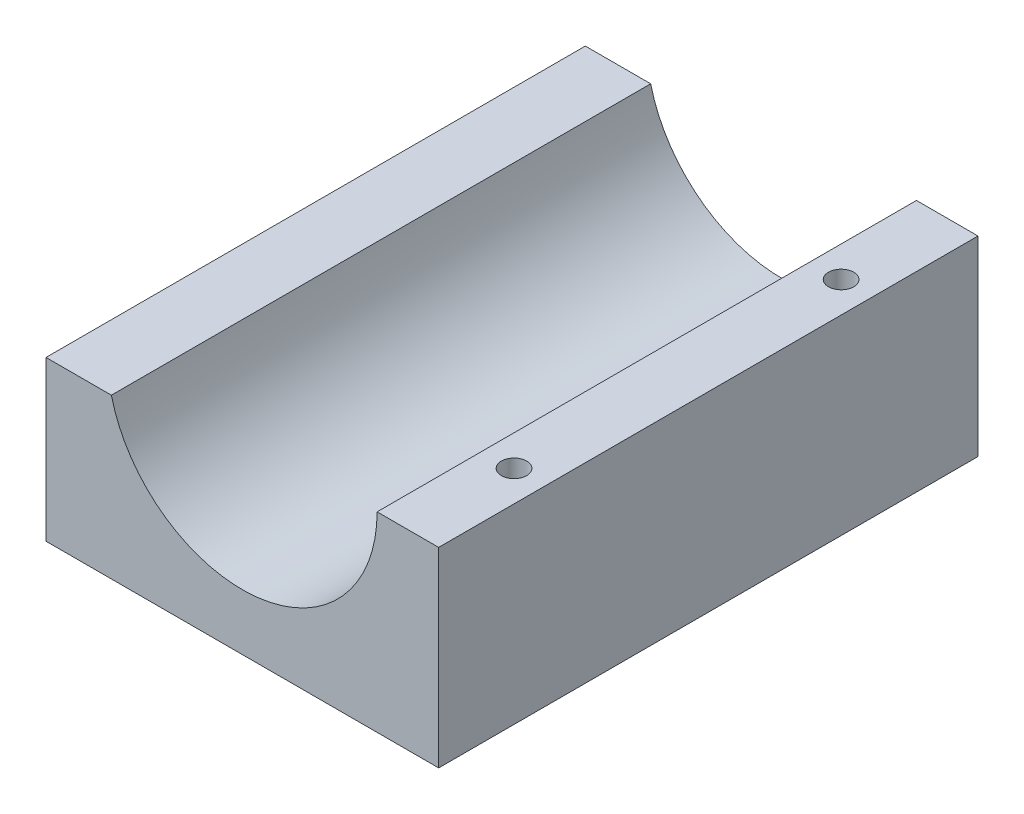
SolidWorks part; units mm, degrees
ref_plane "Front Plane" through (0, 0, 0) normal (0, 0, 1) x (1, 0, 0)
ref_plane "Top Plane" through (0, 0, 0) normal (0, 1, 0) x (1, 0, 0)
ref_plane "Right Plane" through (0, 0, 0) normal (1, 0, 0) x (0, 0, -1)
sketch "Sketch2" plane through (0, 0, 0) normal (0, 1, 0) x (1, 0, 0)
  line L1 (0, 0) -> (18.5, 0)
  line L2 (0, 0) -> (0, 25.41)
  line L3 (0, 25.41) -> (18.5, 25.41)
  line L4 (18.5, 0) -> (18.5, 25.41)
extrude "Boss-Extrude1" add sketch "Sketch2" along normal blind 9
sketch "Sketch6" plane through (0, 0, 0) normal (0, 0, 1) x (1, 0, 0)
  line L0 (0, 9) -> (18.5, 9) construction
  line L1 (2.9, 9) -> (15.6, 9)
  arc A0 (2.9, 9) -> (15.6, 9) centre (9.25, 9) ccw
extrude "Cut-Extrude1" cut sketch "Sketch6" against normal blind 25.41
sketch "Sketch7" plane through (0, 0, 0) normal (0, -1, 0) x (-1, 0, 0)
  line L0 (0, 0) -> (0, 5)
  line L1 (0, 25.41) -> (0, 0) construction
  line L2 (0, 5) -> (-18.5, 5)
  line L3 (-18.5, 0) -> (-18.5, 25.41) construction
  line L4 (0, 25.41) -> (0, 20.41)
  line L5 (0, 20.41) -> (-18.5, 20.41)
sketch "Sketch10" plane through (0, 9, 0) normal (0, 1, 0) x (1, 0, 0)
  line L0 (17.05, 25.41) -> (17.05, 20.41)
  line L1 (18.5, 25.41) -> (15.6, 25.41) construction
  line L2 (17.05, 0) -> (17.05, 5)
  line L3 (15.6, 0) -> (18.5, 0) construction
hole_wizard "#0-80 Tapped Hole1" positions "Sketch11" profile "Sketch12" tap size "#0-80" standard "ANSI Inch"
sketch "Sketch11" plane through (0, 9, 0) normal (0, 1, 0) x (1, 0, 0)
  point P0 (17.05, 20.41)
  point P3 (17.05, 5)
sketch "Sketch12" plane through (17.05, 9, -20.41) normal (1, 0, 0) x (0, 0, 1)
  line L0 (0, 0) -> (0, 4)
  line L1 (0, 4) -> (0.5956, 3.6421)
  line L2 (0.5956, 3.6421) -> (0.5956, 0)
  line L5 (0.5956, 0) -> (0, 0)
  line L10 (0, 4) -> (-0.5956, 3.6421) construction
  line L11 (0, -6.35) -> (0, 107.95) construction
  dimension "Tap Drill Dia." = 1.1913
  dimension "Tap Drill Depth" = 4
  dimension "Drill Angle" = 118
cosmetic thread "Hole Thread3" parameters "D1"=3.05, "D2"=1.524
cosmetic thread "Hole Thread4" parameters "D1"=3.05, "D2"=1.524
sketch "Sketch14" plane through (0, 0, -25.41) normal (0, 0, -1) x (-1, 0, 0)
  line L0 (0, 9) -> (0, 7.5)
  line L1 (0, 9) -> (0, 0) construction
  line L2 (0, 7.5) -> (-3.2467, 7.5)
  line L3 (-3.2467, 7.5) -> (-2.9, 9)
extrude "Cut-Extrude3" cut sketch "Sketch14" against normal blind 25.41 and the other way through all flip side to cut
sketch "Sketch15" plane through (0, 0, 0) normal (0, -1, 0) x (-1, 0, 0)
  line L0 (0, 12.705) -> (-18.5, 12.705)
  line L1 (0, 25.41) -> (0, 0) construction
  line L2 (-18.5, 0) -> (-18.5, 25.41) construction
  line L3 (0, 12.705) -> (-1.5, 12.705)
  line L4 (-18.5, 12.705) -> (-17, 12.705)
hole_wizard "#2-56 Tapped Hole3" positions "Sketch16" profile "Sketch17" tap size "#2-56" standard "ANSI Inch"
sketch "Sketch16" plane through (0, 0, 0) normal (0, -1, 0) x (-1, 0, 0)
  point P0 (-17, 12.705)
  point P3 (-1.5, 12.705)
sketch "Sketch17" plane through (17, 0, -12.705) normal (1, 0, 0) x (0, 0, -1)
  line L0 (0, 0) -> (0, 4)
  line L1 (0, 4) -> (0.889, 3.4658)
  line L2 (0.889, 3.4658) -> (0.889, 0)
  line L5 (0.889, 0) -> (0, 0)
  line L10 (0, 4) -> (-0.889, 3.4658) construction
  line L11 (0, -6.35) -> (0, 107.95) construction
  dimension "Tap Drill Dia." = 1.778
  dimension "Tap Drill Depth" = 4
  dimension "Drill Angle" = 118
cosmetic thread "Hole Thread5" parameters "D1"=4.37, "D2"=2.1844
cosmetic thread "Hole Thread6" parameters "D1"=4.37, "D2"=2.1844
